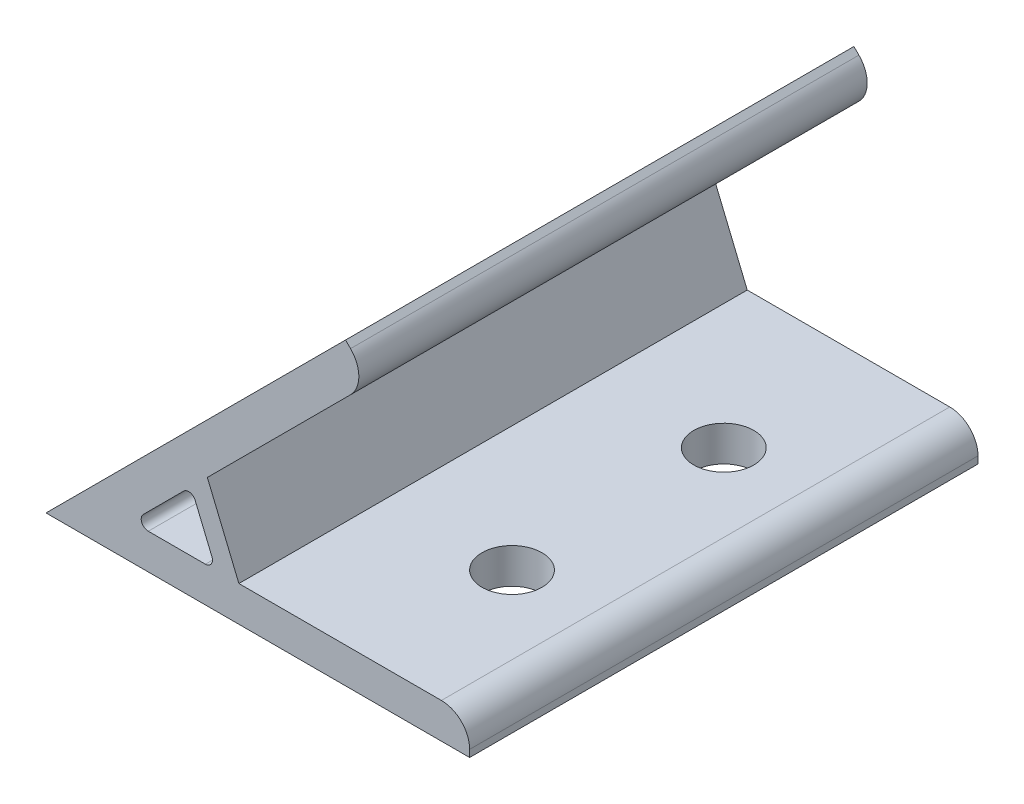
SolidWorks part; units mm, degrees
material "6063 T5"
ref_plane "Спереди" through (0, 0, 0) normal (0, 0, 1) x (1, 0, 0)
ref_plane "Сверху" through (0, 0, 0) normal (0, 1, 0) x (1, 0, 0)
ref_plane "Справа" through (0, 0, 0) normal (1, 0, 0) x (0, 0, -1)
sketch "Эскиз1" plane through (0, 0, 0) normal (0, 0, 1) x (1, 0, 0)
  line L0 (0, 0) -> (42.4264, 42.4264)
  line L1 (42.4264, 42.4264) -> (45.9619, 38.8909)
  line L2 (45.9619, 38.8909) -> (22.8524, 15.7814)
  line L3 (22.8524, 15.7814) -> (27.3182, 5)
  line L4 (27.3182, 5) -> (60, 5)
  line L5 (60, 5) -> (60, 0)
  line L6 (60, 0) -> (0, 0)
  line L7 (20.5563, 13.4853) -> (24.0711, 5)
  line L8 (24.0711, 5) -> (12.0711, 5)
  line L9 (12.0711, 5) -> (20.5563, 13.4853)
  line L10 (18.0711, 5) -> (18.0711, 0) construction
  line L11 (16.3137, 9.2426) -> (12.7782, 12.7782) construction
  line L12 (0, 0) -> (22.3137, 9.2426) construction
  dimension "D1" = 60
  dimension "D2" = 45
  dimension "D4" = 5
  dimension "D5" = 3
  dimension "D6" = 12
extrude "Бобышка-Вытянуть1" add sketch "Эскиз1" along normal mid plane 72
sketch "Эскиз2" plane through (0, 0, 0) normal (-0.7071, 0.7071, 0) x (0, 0, 1)
  line L0 (36, 60) -> (-36, 60) construction
  line L1 (-20, 45) -> (20, 45) construction
  line L2 (-36, 60) -> (-36, 0) construction
  circle A0 centre (-20, 45) radius 4.25
  circle A1 centre (20, 45) radius 4.25
  point P2 (0, 45)
  dimension "D1" = 8.5
  dimension "D2" = 15
  dimension "D4" = 16
  dimension "D3" = 40
extrude "Вырез-Вытянуть1" cut sketch "Эскиз2" against normal up to surface (5 mm away) up to face at (34.4072, 27.3361, 0)
sketch "Эскиз3" plane through (0, 0, 0) normal (0, -1, 0) x (1, 0, 0)
  line L0 (60, 36) -> (60, -36) construction
  line L1 (45, 15) -> (45, -15) construction
  circle A0 centre (45, 15) radius 4.25
  circle A1 centre (45, -15) radius 4.25
  point P2 (45, 0)
  dimension "D1" = 8.5
  dimension "D2" = 15
  dimension "D3" = 30
extrude "Вырез-Вытянуть2" cut sketch "Эскиз3" against normal up to surface (5 mm away) up to face at (43.6591, 5, 0)
fillet "Скругление1" radius 4 2 edges at (60, 5, 0) (45.9619, 38.8909, 0)
fillet "Скругление2" radius 1 3 edges at (20.5563, 13.4853, 0) (12.0711, 5, 0) (24.0711, 5, 0)
